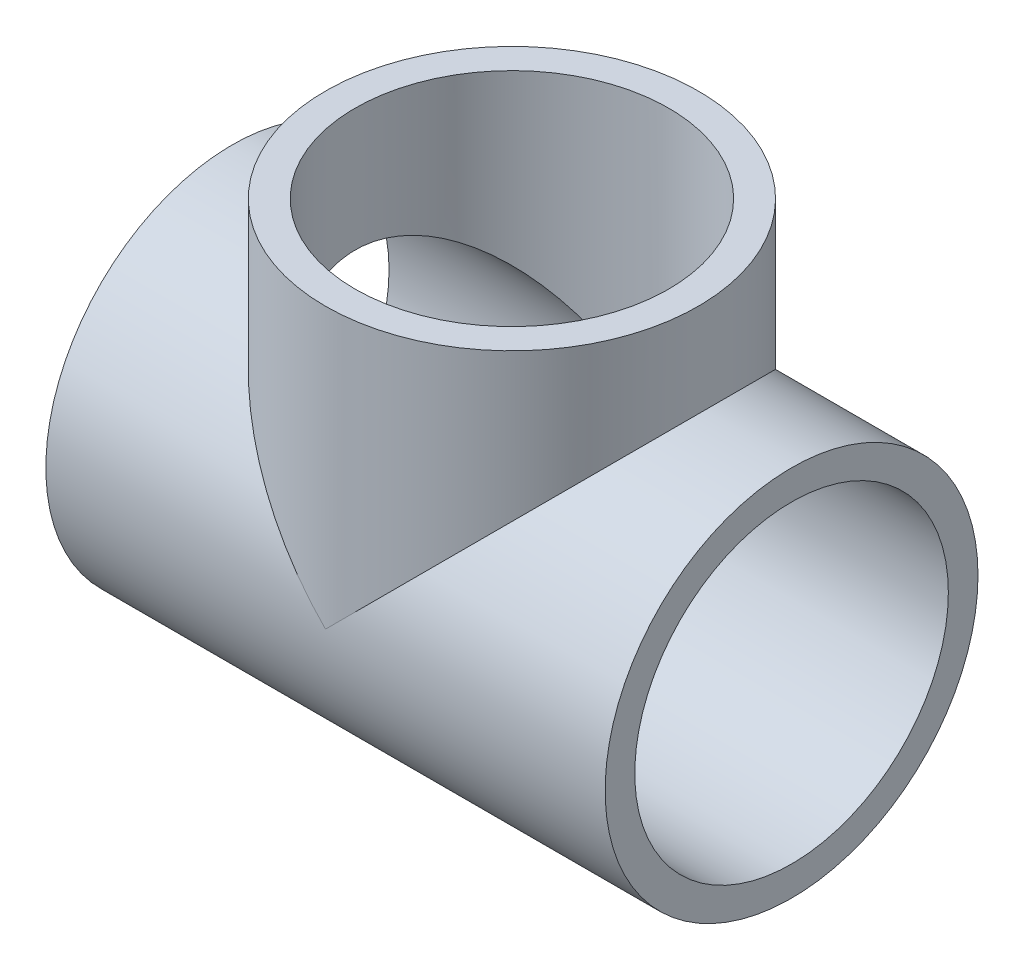
SolidWorks part; units mm, degrees
material "PVC 0.007 Plasticized"
ref_plane "Front Plane" through (0, 0, 0) normal (0, 0, 1) x (1, 0, 0)
ref_plane "Top Plane" through (0, 0, 0) normal (0, 1, 0) x (1, 0, 0)
ref_plane "Right Plane" through (0, 0, 0) normal (1, 0, 0) x (0, 0, -1)
sketch "Sketch2" plane through (0, 0, 0) normal (1, 0, 0) x (0, 0, -1)
  circle A0 centre (0, 0) radius 12.7
  circle A1 centre (0, 0) radius 10.6807
  dimension "D1" = 25.4
  dimension "D2" = 21.3614
extrude "Boss-Extrude1" add sketch "Sketch2" against normal mid plane 38.1
ref_plane "Plane1" through (0, 19.05, 0) normal (0, 1, 0) x (1, 0, 0)
sketch "Sketch4" plane through (0, 0, 0) normal (1, 0, 0) x (0, 0, -1)
  line L0 (0, 0) -> (0, 26.1788) construction
sketch "Sketch5" plane through (0, 19.05, 0) normal (0, 1, 0) x (1, 0, 0)
  circle A0 centre (0, 0) radius 12.7
  point P2 (0, 0)
  dimension "D1" = 25.4
extrude "Boss-Extrude2" add sketch "Sketch5" against normal up to surface (19.05 mm away) up to face at (-19.05, 0, -12.7)
sketch "Sketch6" plane through (0, 19.05, 0) normal (0, 1, 0) x (1, 0, 0)
  circle A0 centre (0, 0) radius 10.6807
  dimension "D1" = 21.3614
extrude "Cut-Extrude1" cut sketch "Sketch6" against normal up to next
